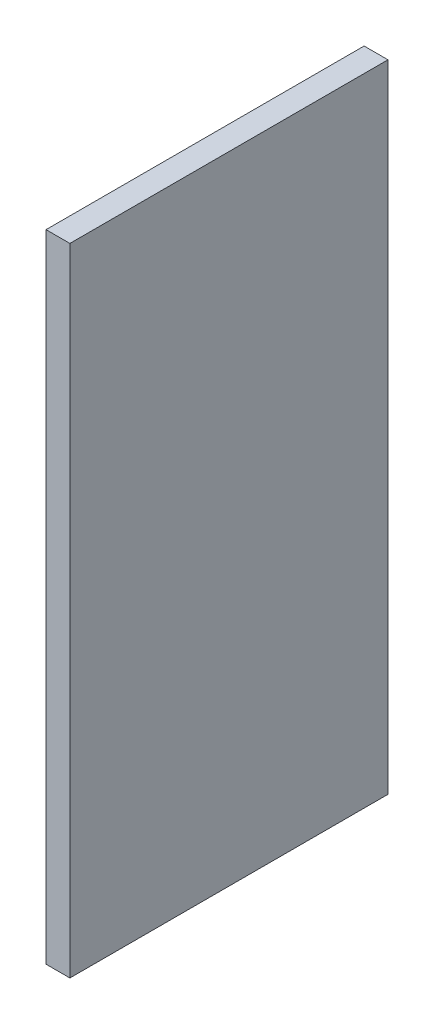
SolidWorks part; units mm, degrees
material "PMMA"
ref_plane "Plan de face" through (0, 0, 0) normal (0, 0, 1) x (1, 0, 0)
ref_plane "Plan de dessus" through (0, 0, 0) normal (0, 1, 0) x (1, 0, 0)
ref_plane "Plan de droite" through (0, 0, 0) normal (1, 0, 0) x (0, 0, -1)
sketch "Esquisse2" plane through (0, 0, 0) normal (0, 0, 1) x (1, 0, 0)
  line L1 (0, 160) -> (6, 160)
  line L2 (0, 160) -> (0, 0)
  line L3 (0, 0) -> (6, 0)
  line L4 (6, 160) -> (6, 0)
  dimension "D1" = 160
  dimension "D2" = 6
extrude "Boss.-Extru.1" add sketch "Esquisse2" along normal blind 80
